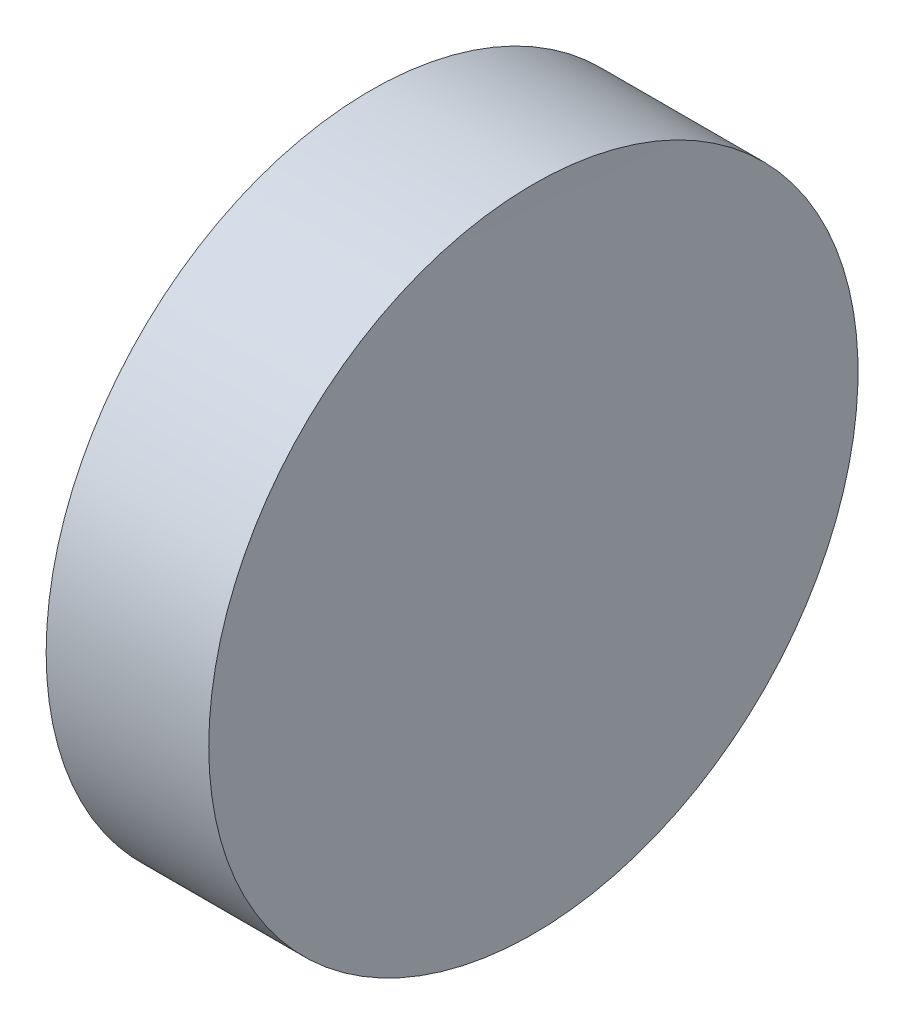
SolidWorks part; units mm, degrees
ref_plane "前视基准面" through (0, 0, 0) normal (0, 0, 1) x (1, 0, 0)
ref_plane "上视基准面" through (0, 0, 0) normal (0, 1, 0) x (1, 0, 0)
ref_plane "右视基准面" through (0, 0, 0) normal (1, 0, 0) x (0, 0, -1)
sketch "草图1" plane through (0, 0, 0) normal (0, 1, 0) x (1, 0, 0)
  line L0 (0, 0) -> (6.9328, 0) construction
  line L1 (0, 0) -> (3.14, 0)
  line L2 (0, 0) -> (0, 6.35)
  line L3 (0, 6.35) -> (3.1803, 6.35)
  arc A0 (3.1803, 6.35) -> (3.14, 0) centre (503.14, 0) ccw
  dimension "D3" = 500
  dimension "D1" = 3.14
  dimension "D2" = 6.35
revolve "旋转1" add sketch "草图1" angle 360 about L0
